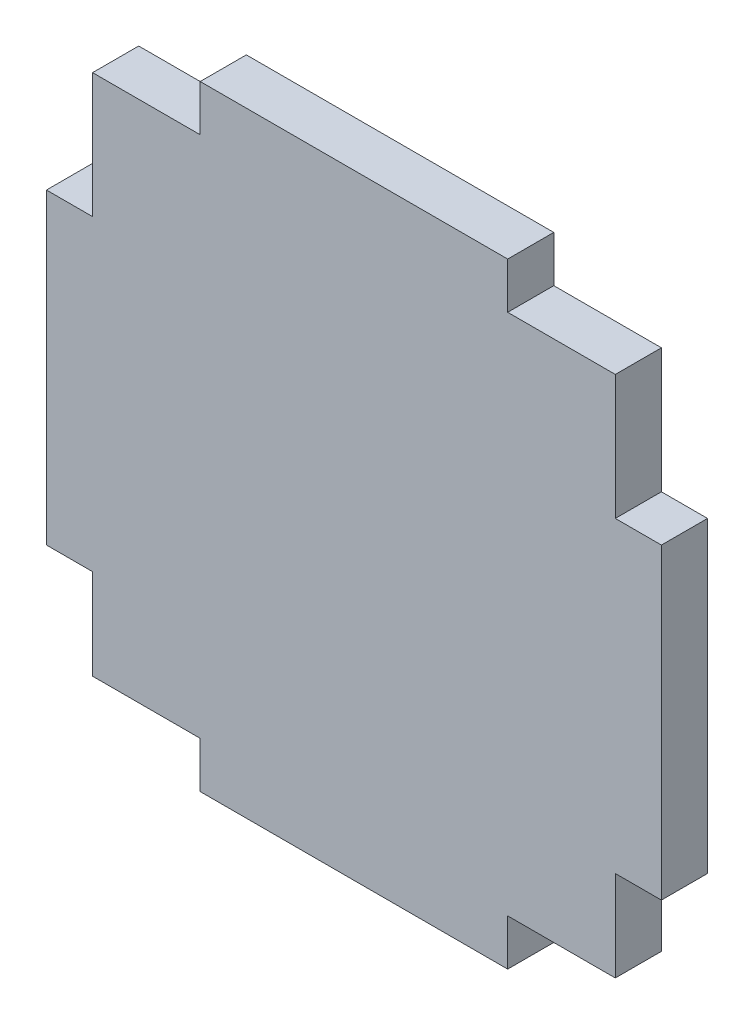
SolidWorks part; units mm, degrees
ref_plane "Alzado" through (0, 0, 0) normal (0, 0, 1) x (1, 0, 0)
ref_plane "Planta" through (0, 0, 0) normal (0, 1, 0) x (1, 0, 0)
ref_plane "Vista lateral" through (0, 0, 0) normal (1, 0, 0) x (0, 0, -1)
sketch "Croquis1" plane through (0, 0, 0) normal (0, 0, 1) x (1, 0, 0)
  line L0 (83.7739, -19.6986) -> (83.7739, -16.6986)
  line L1 (103.7739, -19.6986) -> (103.7739, -16.6986)
  line L2 (83.7739, -16.6986) -> (103.7739, -16.6986)
  line L3 (103.7739, -53.6986) -> (103.7739, -56.6986)
  line L4 (83.7739, -56.6986) -> (103.7739, -56.6986)
  line L5 (83.7739, -53.6986) -> (83.7739, -56.6986)
  line L6 (110.7739, -19.6986) -> (110.7739, -27.8105)
  line L7 (73.7739, -27.8105) -> (76.7739, -27.8105)
  line L8 (113.7739, -27.8105) -> (110.7739, -27.8105)
  line L9 (73.7739, -47.8105) -> (76.7739, -47.8105)
  line L10 (113.7739, -47.8105) -> (110.7739, -47.8105)
  line L11 (110.7739, -47.8105) -> (110.7739, -53.6986)
  line L12 (76.7739, -47.8105) -> (76.7739, -53.6986)
  line L13 (76.7739, -27.8105) -> (76.7739, -19.6986)
  line L14 (76.7739, -19.6986) -> (83.7739, -19.6986)
  line L15 (73.7739, -27.8105) -> (73.7739, -47.8105)
  line L16 (76.7739, -53.6986) -> (83.7739, -53.6986)
  line L17 (103.7739, -19.6986) -> (110.7739, -19.6986)
  line L18 (113.7739, -27.8105) -> (113.7739, -47.8105)
  line L19 (103.7739, -53.6986) -> (110.7739, -53.6986)
  point P6 (0, 0)
  point P10 (93.7739, -58.9225)
  point P22 (0, 0)
  dimension "D1" = 3
  dimension "D2" = 3
  dimension "D3" = 20
  dimension "D4" = 20
  dimension "D5" = 20
  dimension "D6" = 20
  dimension "D7" = 40
  dimension "D8" = 40
  dimension "D9" = 3
  dimension "D10" = 3
  dimension "D11" = 3
  dimension "D12" = 3
  dimension "D13" = 34
  dimension "D14" = 34
extrude "Saliente-Extruir1" add sketch "Croquis1" along normal blind 3
